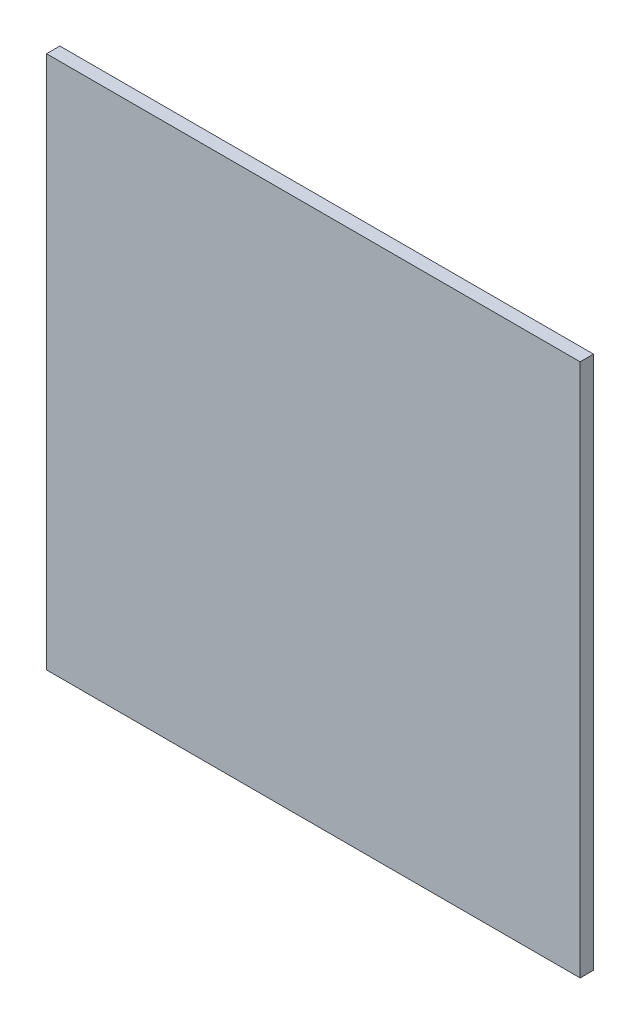
SolidWorks part; units mm, degrees
material "Alloy Steel"
ref_plane "Front Plane" through (0, 0, 0) normal (0, 0, 1) x (1, 0, 0)
ref_plane "Top Plane" through (0, 0, 0) normal (0, 1, 0) x (1, 0, 0)
ref_plane "Right Plane" through (0, 0, 0) normal (1, 0, 0) x (0, 0, -1)
sketch "Sketch2" plane through (0, 0, 0) normal (0, 0, 1) x (1, 0, 0)
  line L1 (-400, -400) -> (400, -400)
  line L2 (-400, -400) -> (-400, 400)
  line L3 (-400, 400) -> (400, 400)
  line L4 (400, -400) -> (400, 400)
  line L5 (-400, -400) -> (400, 400) construction
  line L6 (-400, 400) -> (400, -400) construction
  point P0 (0, 0)
  point P6 (0, 0)
extrude "Boss-Extrude1" add sketch "Sketch2" along normal blind 20
